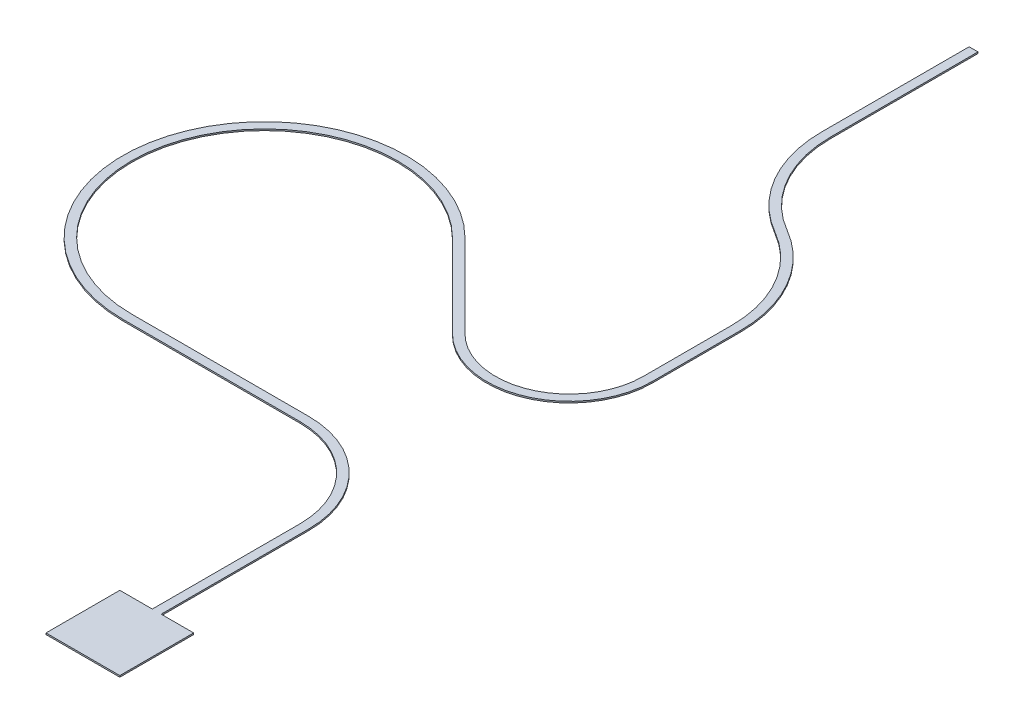
SolidWorks part; units mm, degrees
ref_plane "Front Plane" through (0, 0, 0) normal (0, 0, 1) x (1, 0, 0)
ref_plane "Top Plane" through (0, 0, 0) normal (0, 1, 0) x (1, 0, 0)
ref_plane "Right Plane" through (0, 0, 0) normal (1, 0, 0) x (0, 0, -1)
sketch "Sketch1" plane through (0, 0, 0) normal (0, 1, 0) x (1, 0, 0)
  line L0 (-315, 955) -> (-915, 955)
  line L2 (-125, 125) -> (-125, -125)
  line L3 (-125, -125) -> (125, -125)
  line L4 (125, 125) -> (125, -125)
  line L5 (-125, 125) -> (125, -125) construction
  line L6 (-125, -125) -> (125, 125) construction
  line L8 (15, 125) -> (15, 625)
  line L10 (-15, 125) -> (-15, 625)
  line L11 (-315, 925) -> (-915, 925)
  line L12 (-125, 125) -> (-15, 125)
  line L13 (-575.5887, 1744.4113) -> (-292.746, 1461.5685)
  line L14 (-596.8019, 1723.1981) -> (-313.9592, 1440.3553)
  line L16 (164.0307, 1638.3452) -> (164.0307, 1938.3452)
  line L17 (134.0307, 1638.3452) -> (134.0307, 1938.3452)
  line L18 (-250.9693, 2657.1463) -> (-250.9693, 3157.1463)
  line L19 (-280.9693, 2657.1463) -> (-280.9693, 3157.1463)
  line L20 (-280.9693, 3157.1463) -> (-250.9693, 3157.1463)
  line L21 (15, 125) -> (125, 125)
  arc A0 (-15, 625) -> (-315, 925) centre (-315, 625) ccw
  arc A1 (15, 625) -> (-315, 955) centre (-315, 625) ccw
  arc A2 (-915, 955) -> (-596.8019, 1723.1981) centre (-915, 1405) cw
  arc A3 (-915, 925) -> (-575.5887, 1744.4113) centre (-915, 1405) cw
  arc A4 (-292.746, 1461.5685) -> (134.0307, 1638.3452) centre (-115.9693, 1638.3452) ccw
  arc A5 (-313.9592, 1440.3553) -> (164.0307, 1638.3452) centre (-115.9693, 1638.3452) ccw
  arc A6 (134.0307, 1938.3452) -> (-65.9693, 2284.7554) centre (-265.9693, 1938.3452) ccw
  arc A7 (164.0307, 1938.3452) -> (-50.9693, 2310.7362) centre (-265.9693, 1938.3452) ccw
  arc A8 (-50.9693, 2310.7362) -> (-250.9693, 2657.1463) centre (149.0307, 2657.1463) cw
  arc A9 (-65.9693, 2284.7554) -> (-280.9693, 2657.1463) centre (149.0307, 2657.1463) cw
  point P0 (0, 0)
  dimension "D7" = 300
  dimension "D8" = 330
  dimension "D10" = 450
  dimension "D11" = 480
  dimension "D16" = 250
  dimension "D17" = 280
  dimension "D20" = 400
  dimension "D22" = 430
  dimension "D24" = 400
  dimension "D25" = 430
  dimension "D1" = 250
  dimension "D2" = 250
  dimension "D3" = 30
  dimension "D4" = 110
  dimension "D5" = 500
  dimension "D6" = 600
  dimension "D9" = 30
  dimension "D12" = 135
  dimension "D13" = 135
  dimension "D14" = 400
  dimension "D15" = 400
  dimension "D18" = 300
  dimension "D19" = 300
  dimension "D21" = 60
  dimension "D23" = 60
  dimension "D26" = 500
  dimension "D27" = 500
  dimension "D28" = 125
extrude "Boss-Extrude1" add sketch "Sketch1" along normal blind 5
